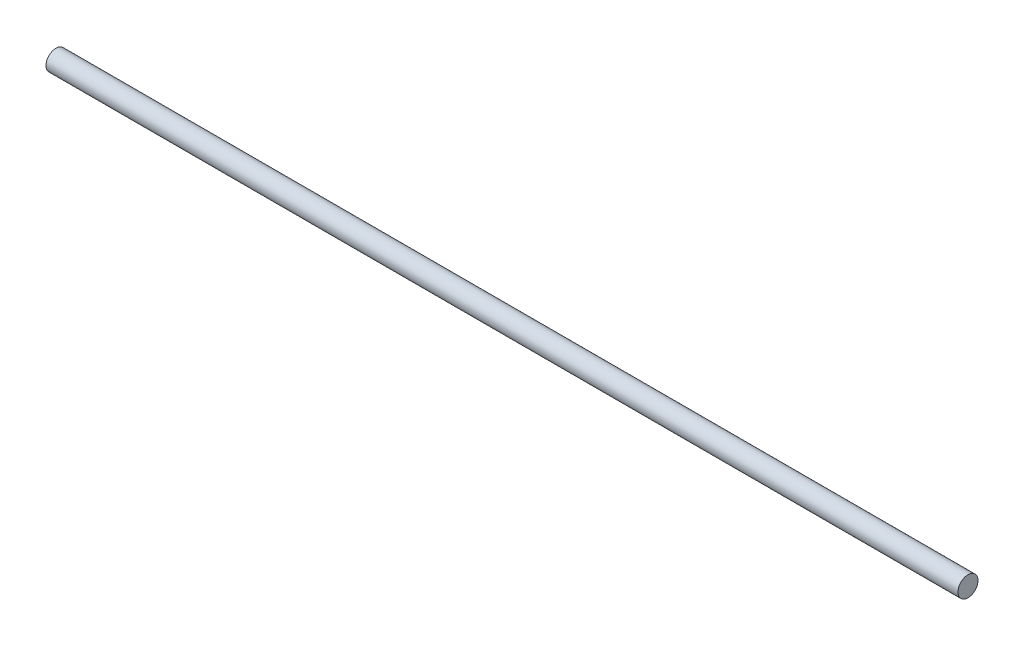
SolidWorks part; units mm, degrees
ref_plane "Front Plane" through (0, 0, 0) normal (0, 0, 1) x (1, 0, 0)
ref_plane "Top Plane" through (0, 0, 0) normal (0, 1, 0) x (1, 0, 0)
ref_plane "Right Plane" through (0, 0, 0) normal (1, 0, 0) x (0, 0, -1)
sketch "Sketch1" plane through (0, 0, 0) normal (1, 0, 0) x (0, 0, -1)
  circle A0 centre (0, 0) radius 1.5875
  dimension "D1" = 3.175
extrude "Boss-Extrude1" add sketch "Sketch1" along normal mid plane 144.6022
